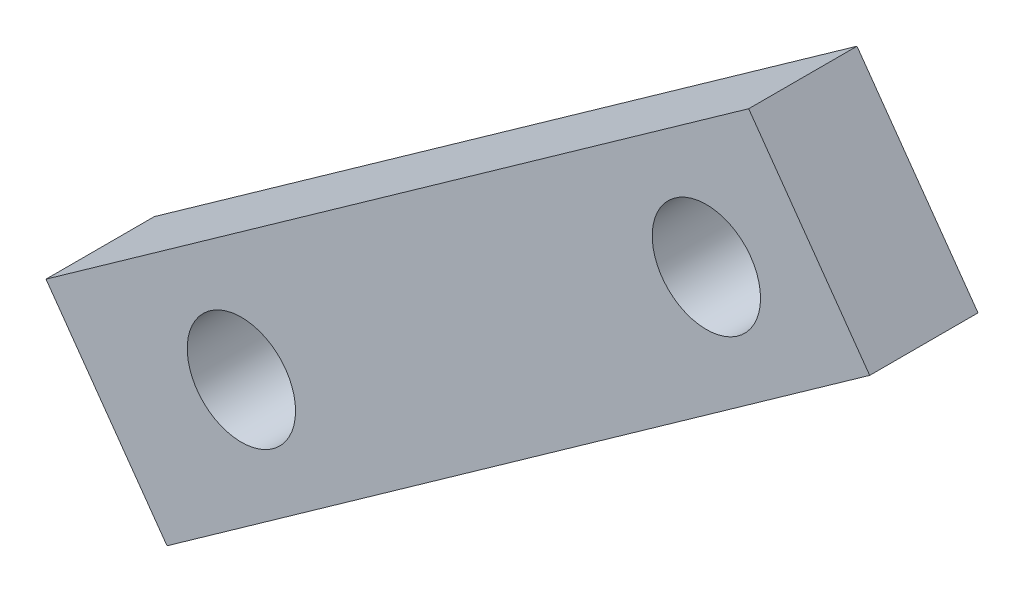
SolidWorks part; units mm, degrees
ref_plane "Front Plane" through (0, 0, 0) normal (0, 0, 1) x (1, 0, 0)
ref_plane "Top Plane" through (0, 0, 0) normal (0, 1, 0) x (1, 0, 0)
ref_plane "Right Plane" through (0, 0, 0) normal (1, 0, 0) x (0, 0, -1)
sketch "Sketch1" plane through (0, 0, 0) normal (0, 0, 1) x (1, 0, 0)
  line L0 (-36.3748, -6.4424) -> (-19.8959, 5.2576)
  line L1 (-36.3748, -6.4424) -> (-33.5368, -10.4395)
  line L2 (-33.5368, -10.4395) -> (-17.0579, 1.2605)
  line L3 (-17.0579, 1.2605) -> (-19.8959, 5.2576)
  line L4 (-33.2112, -4.1963) -> (-30.3733, -8.1934)
  line L5 (-34.9558, -8.4409) -> (-18.4769, 3.2591)
  line L6 (-22.301, 3.55) -> (-19.475, -0.4556)
  circle A0 centre (-31.7923, -6.1948) radius 1.27
  circle A2 centre (-20.888, 1.5472) radius 1.27
extrude "Boss-Extrude1" add sketch "Sketch1" along normal blind 2.54 contours A2 L5 L3 L0 L6 | A2 L6 L2 L3 L5 | A2 L5 A0 L4 L2 L6 | A2 L6 L0 L4 A0 L5 | A0 L4 L0 L1 L5 | A0 L5 L1 L2 L4
